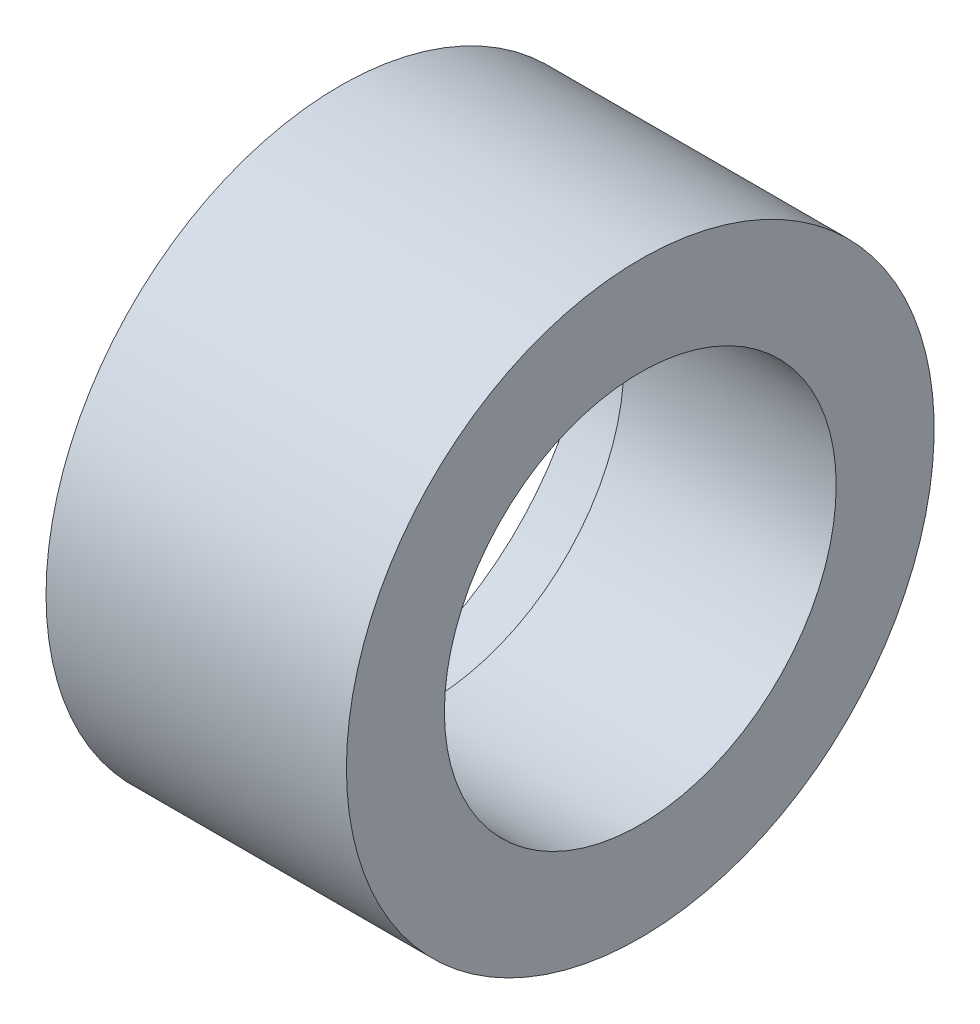
SolidWorks part; units mm, degrees
material "AISI 316 Annealed Stainless Steel Bar (SS)"
ref_plane "Front Plane" through (0, 0, 0) normal (0, 0, 1) x (1, 0, 0)
ref_plane "Top Plane" through (0, 0, 0) normal (0, 1, 0) x (1, 0, 0)
ref_plane "Right Plane" through (0, 0, 0) normal (1, 0, 0) x (0, 0, -1)
sketch "Sketch3" plane through (0, 0, 0) normal (0, 0, 1) x (1, 0, 0)
  line L0 (-58.5481, 189.9573) -> (284.033, 189.9573) construction
  line L2 (213.4012, -189.6279) -> (558.7345, -189.6279) construction
  line L4 (227.3705, -148.5737) -> (308.4812, -148.5737) construction
  line L33 (253.3852, -142.5737) -> (253.3852, -140.8737)
  line L38 (250.6852, -139.5737) -> (259.8852, -139.5737)
  line L87 (250.6852, -140.8737) -> (253.3852, -140.8737)
  line L93 (259.8852, -139.5737) -> (259.8852, -140.8572)
  line L95 (250.6852, -139.5737) -> (250.6852, -140.8737)
  line L96 (253.3852, -142.5737) -> (259.8852, -142.5737)
  line L97 (259.8852, -142.5737) -> (259.8852, -140.8572)
  line L112 (261.9184, -141.0941) -> (261.9184, -140.8247)
  dimension "D1" = 9
  dimension "D2" = 9.2
  dimension "D3" = 7.7
  dimension "D4" = 2.7
  dimension "D6" = 6
revolve "Revolve1" add sketch "Sketch3" angle 360 about L4
sketch3d "3DSketch1"
  line L0 (259.8852, -148.5737, 0) -> (253.3852, -148.5737, 0) construction
  line L1 (253.3852, -148.5737, 0) -> (253.3852, -140.6737, 0) construction
  line L2 (259.8852, -148.5737, 0) -> (259.8852, -144.8601, 0) construction
  line L3 (259.8852, -144.8601, 0) -> (253.3852, -140.6737, 0)
  circle A0 centre (259.8852, -148.5737, 0) radius 3.7136 construction
  circle A2 centre (253.3852, -148.5737, 0) radius 7.9 construction
  point P2 (263.5987, -148.5737, 0)
  point P7 (245.4852, -148.5737, 0)
